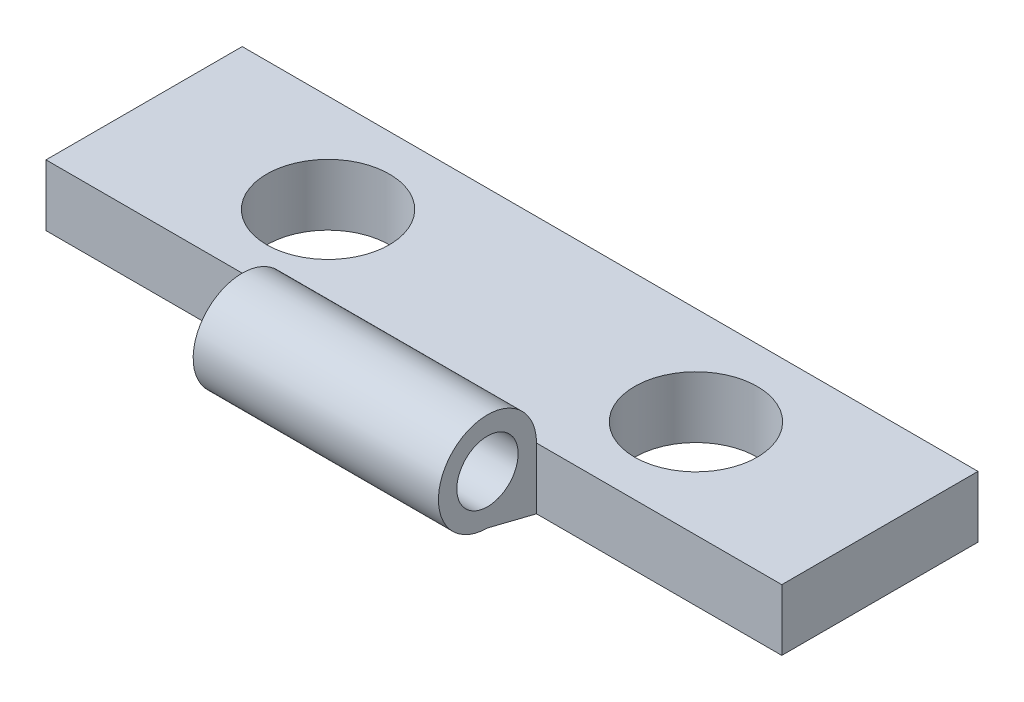
SolidWorks part; units mm, degrees
material "1060 Alloy"
ref_plane "Front Plane" through (0, 0, 0) normal (0, 0, 1) x (1, 0, 0)
ref_plane "Top Plane" through (0, 0, 0) normal (0, 1, 0) x (1, 0, 0)
ref_plane "Right Plane" through (0, 0, 0) normal (1, 0, 0) x (0, 0, -1)
sketch "Sketch1" plane through (0, 0, 0) normal (0, 1, 0) x (1, 0, 0)
  line L1 (-15, -4) -> (15, -4)
  line L2 (-15, -4) -> (-15, 4)
  line L3 (-15, 4) -> (15, 4)
  line L4 (15, -4) -> (15, 4)
  line L5 (-15, -4) -> (15, 4) construction
  line L6 (-15, 4) -> (15, -4) construction
  circle A0 centre (-7.5, 0) radius 2.5
  circle A1 centre (7.5, 0) radius 2.5
  point P0 (0, 0)
  dimension "D5" = 5
  dimension "D1" = 30
  dimension "D2" = 8
  dimension "D3" = 7.5
  dimension "D4" = 7.5
extrude "Boss-Extrude1" add sketch "Sketch1" along normal blind 2.5
sketch "Sketch2" plane through (0, 0, 0) normal (1, 0, 0) x (0, 0, -1)
  line L0 (0, 0) -> (0, 2.5) construction
  line L1 (-4, 2.5) -> (4, 2.5) construction
  line L5 (-4, 2.5) -> (-4, 0)
  line L6 (-4, 0) -> (-6, 0.5)
  circle A1 centre (-6, 2.5) radius 1.25
  arc A2 (-4, 2.5) -> (-6, 0.5) centre (-6, 2.5) ccw
  dimension "D1" = 4
  dimension "D2" = 2.5
extrude "Boss-Extrude2" add sketch "Sketch2" along normal up to surface and the other way up to surface up to face at (15, 1.25, 0) other way up to face at (-15, 1.25, 0)
sketch "Sketch4" plane through (0, 0, 0) normal (0, 1, 0) x (1, 0, 0)
  line L0 (-15, -4) -> (15, -4) construction
  line L2 (-5, -4) -> (-5, -8)
  line L4 (5, -4) -> (5, -8)
  line L5 (-15, -8) -> (15, -8) construction
  line L6 (15, -8) -> (15, -4) construction
  line L15 (5, -4) -> (15, -4)
  line L16 (-15, -4) -> (-5, -4)
  line L17 (-15, -4) -> (-15, -8)
  line L18 (-15, -8) -> (-5, -8)
  line L19 (15, -4) -> (15, -8)
  line L20 (5, -8) -> (15, -8)
  dimension "D1" = 10
  dimension "D2" = 10
extrude "Cut-Extrude2" cut sketch "Sketch4" along normal through all
